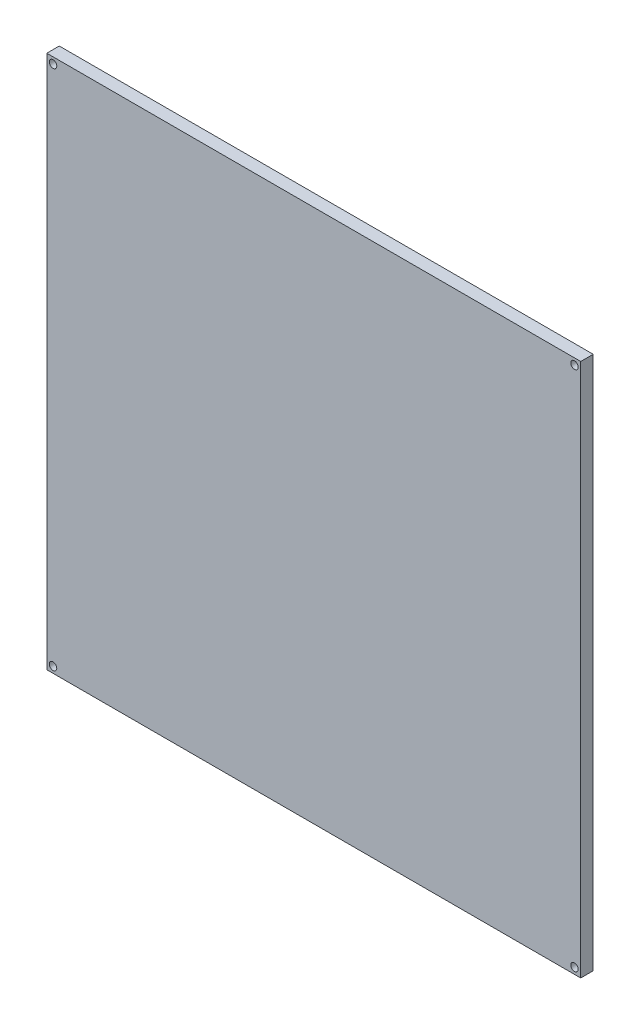
SolidWorks part; units mm, degrees
ref_plane "Piano frontale" through (0, 0, 0) normal (0, 0, 1) x (1, 0, 0)
ref_plane "Piano superiore" through (0, 0, 0) normal (0, 1, 0) x (1, 0, 0)
ref_plane "Piano destro" through (0, 0, 0) normal (1, 0, 0) x (0, 0, -1)
sketch "Schizzo1" plane through (0, 0, 0) normal (0, 0, 1) x (1, 0, 0)
  line L0 (214, 107) -> (0, 107) construction
  line L1 (0, 0) -> (214, 0)
  line L2 (0, 0) -> (0, 214)
  line L3 (0, 214) -> (214, 214)
  line L4 (214, 0) -> (214, 214)
  line L5 (107, 214) -> (107, 0) construction
  line L6 (-11.5957, 211.5) -> (76.5579, 211.5) construction
  line L7 (2.5, 220.8655) -> (2.5, 195.39) construction
  circle A0 centre (2.5, 211.5) radius 1.5
  circle A1 centre (211.5, 211.5) radius 1.5
  circle A2 centre (2.5, 2.5) radius 1.5
  circle A3 centre (211.5, 2.5) radius 1.5
  dimension "D5" = 3
  dimension "D1" = 214
  dimension "D2" = 214
  dimension "D3" = 104.5
  dimension "D4" = 104.5
extrude "Estrusione-Estrusione1" add sketch "Schizzo1" against normal blind 5
